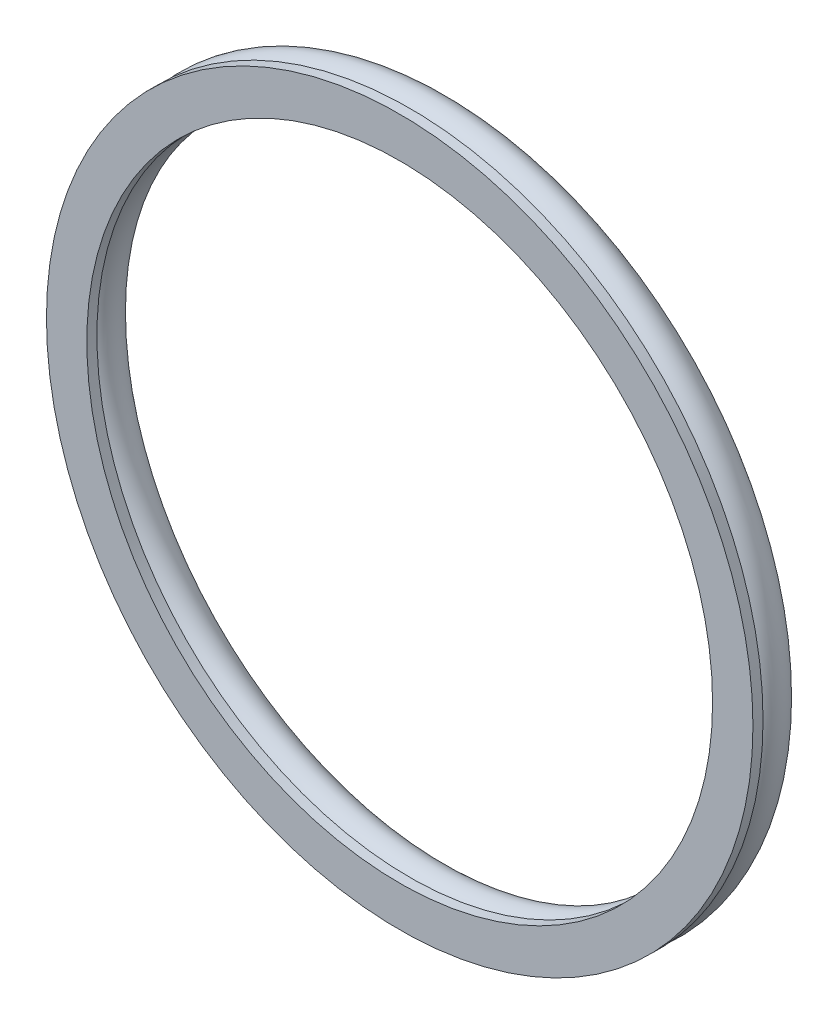
SolidWorks part; units mm, degrees
ref_plane "Front Plane" through (0, 0, 0) normal (0, 0, 1) x (1, 0, 0)
ref_plane "Top Plane" through (0, 0, 0) normal (0, 1, 0) x (1, 0, 0)
ref_plane "Right Plane" through (0, 0, 0) normal (1, 0, 0) x (0, 0, -1)
sketch "Sketch3" plane through (0, 0, 0) normal (1, 0, 0) x (0, 0, -1)
  line L0 (0, 0) -> (282.8835, 0) construction
  line L1 (0, 0) -> (0, 165) construction
  circle A0 centre (0, 165) radius 10
  dimension "D1" = 165
revolve "Revolve1" add sketch "Sketch3" angle 360 about L0
ref_plane "Plane1" through (0, 0, 10) normal (0, 0, 1) x (1, 0, 0)
sketch "Sketch5" plane through (0, 0, 10) normal (0, 0, 1) x (1, 0, 0)
  circle A0 centre (0, 0) radius 175
  circle A1 centre (0, 0) radius 155
extrude "Boss-Extrude1" add sketch "Sketch5" along normal blind 5 separate body
